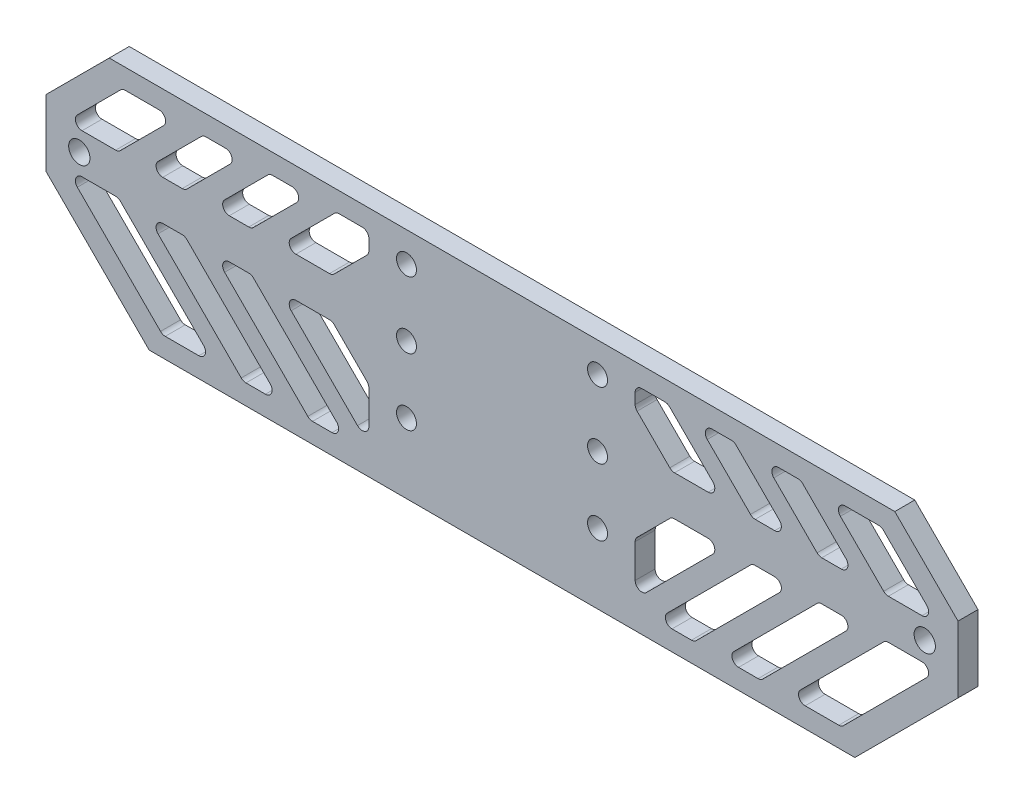
SolidWorks part; units mm, degrees
material "Thornel Mat VMA"
ref_plane "前视基准面" through (0, 0, 0) normal (0, 0, 1) x (1, 0, 0)
ref_plane "上视基准面" through (0, 0, 0) normal (0, 1, 0) x (1, 0, 0)
ref_plane "右视基准面" through (0, 0, 0) normal (1, 0, 0) x (0, 0, -1)
sketch "草图1" plane through (0, 0, 0) normal (0, 0, 1) x (1, 0, 0)
  line L1 (-16.35, 14.5) -> (16.35, 14.5)
  line L2 (-16.35, 14.5) -> (-16.35, -14.5)
  line L3 (-16.35, -14.5) -> (16.35, -14.5)
  line L4 (16.35, 14.5) -> (16.35, -14.5)
  line L5 (-16.35, 14.5) -> (16.35, -14.5) construction
  line L6 (-16.35, -14.5) -> (16.35, 14.5) construction
  line L7 (-14.35, 10) -> (14.35, 10) construction
  line L8 (-14.35, 10) -> (-14.35, -10) construction
  line L9 (-14.35, -10) -> (14.35, -10) construction
  line L10 (14.35, 10) -> (14.35, -10) construction
  line L11 (-14.35, 10) -> (14.35, -10) construction
  line L12 (-14.35, -10) -> (14.35, 10) construction
  circle A0 centre (-14.35, -10) radius 1.5
  circle A1 centre (-14.35, 10) radius 1.5
  circle A2 centre (14.35, 10) radius 1.5
  circle A3 centre (14.35, -10) radius 1.5
  circle A4 centre (-14.35, 0) radius 1.5
  circle A5 centre (14.35, 0) radius 1.5
  point P0 (0, 0)
  point P6 (0, 0)
  dimension "D5" = 3
  dimension "D1" = 29
  dimension "D2" = 28.7
  dimension "D3" = 32.7
  dimension "D4" = 20
extrude "凸台-拉伸1" add sketch "草图1" along normal blind 3
chamfer "倒角1" distance 3 angle 45 4 edges at (16.35, -14.5, 1.5) (16.35, 14.5, 1.5) (-16.35, -14.5, 1.5) (-16.35, 14.5, 1.5)
sketch "草图2" plane through (0, 0, 3) normal (0, 0, 1) x (1, 0, 0)
  line L0 (-11, 7) -> (-8, 10)
  line L1 (-8, 10) -> (8, 10)
  line L2 (-11, 7) -> (-11, -7)
  line L3 (-8, -10) -> (8, -10)
  line L4 (11, 7) -> (11, -7)
  line L5 (-11, 10) -> (11, -10) construction
  line L6 (-11, -10) -> (11, 10) construction
  line L7 (8, 10) -> (11, 7)
  line L8 (-11, -7) -> (-8, -10)
  line L9 (8, -10) -> (11, -7)
  point P0 (0, 0)
  dimension "D1" = 22
  dimension "D2" = 20
extrude "切除-拉伸1" [suppressed] cut sketch "草图2" against normal through all
fillet "圆角1" [suppressed] radius 1
sketch "草图3" plane through (0, 0, 3) normal (0, 0, 1) x (1, 0, 0)
  line L1 (-68.5, 14.5) -> (68.5, 14.5)
  line L2 (-68.5, 14.5) -> (-68.5, -14.5)
  line L3 (-68.5, -14.5) -> (68.5, -14.5)
  line L4 (68.5, 14.5) -> (68.5, -14.5)
  line L5 (-68.5, 14.5) -> (68.5, -14.5) construction
  line L6 (-68.5, -14.5) -> (68.5, 14.5) construction
  line L8 (16.35, -11.5) -> (16.35, 11.5)
  line L9 (16.35, 11.5) -> (13.35, 14.5)
  line L10 (13.35, 14.5) -> (-13.35, 14.5)
  line L11 (-13.35, 14.5) -> (-16.35, 11.5)
  line L12 (-16.35, 11.5) -> (-16.35, -11.5)
  line L13 (-16.35, -11.5) -> (-13.35, -14.5)
  line L14 (-13.35, -14.5) -> (13.35, -14.5)
  line L15 (13.35, -14.5) -> (16.35, -11.5)
  line L16 (16.35, -11.5) -> (16.35, 11.5)
  line L17 (16.35, 11.5) -> (13.35, 14.5)
  line L18 (13.35, 14.5) -> (-13.35, 14.5)
  line L19 (-13.35, 14.5) -> (-16.35, 11.5)
  line L20 (-16.35, 11.5) -> (-16.35, -11.5)
  line L21 (-16.35, -11.5) -> (-13.35, -14.5)
  line L22 (-13.35, -14.5) -> (13.35, -14.5)
  line L23 (13.35, -14.5) -> (16.35, -11.5)
  point P2 (0, 0)
  dimension "D2" = 137
  dimension "D1" = 0
extrude "凸台-拉伸2" add sketch "草图3" against normal up to surface (3 mm away) up to face at (0, 0, 0)
chamfer "倒角2" distance 9.5 4 edges at (68.5, -14.5, 1.5) (68.5, 14.5, 1.5) (-68.5, 14.5, 1.5) (-68.5, -14.5, 1.5)
sketch "草图4" plane through (0, 0, 0) normal (0, 0, -1) x (-1, 0, 0)
  line L0 (-59, -14.5) -> (-53, -20.5)
  line L1 (-53, -20.5) -> (53, -20.5)
  line L2 (53, -20.5) -> (59, -14.5)
  line L3 (59, -14.5) -> (-59, -14.5)
  line L4 (-68.5, -5) -> (-59, -14.5) construction
  line L5 (59, -14.5) -> (68.5, -5) construction
  dimension "D3" = 6
extrude "凸台-拉伸3" add sketch "草图4" against normal up to surface (3 mm away) up to face at (0, 0, 3)
sketch "草图6" plane through (0, 0, 0) normal (0, 0, -1) x (-1, 0, 0)
  circle A0 centre (-63.5, 0) radius 1.6
  dimension "D2" = 3.2
  dimension "D1" = 63.5
extrude "切除-拉伸2" cut sketch "草图6" against normal through all
sketch "草图7" plane through (0, 0, 0) normal (0, 0, -1) x (-1, 0, 0)
  line L24 (-65.5, 3) -> (-57, 11.5)
  line L29 (-65.5, -3) -> (-51, -17.5)
  line L30 (-55.5, -3) -> (-41, -17.5)
  line L32 (-68.5, 0) -> (0, 0)
  line L33 (-68.5, -5) -> (-68.5, 5) construction
  line L34 (-68.5, -3) -> (0, -3)
  line L35 (-68.5, 3) -> (0, 3)
  line L36 (-20, 14.5) -> (-20, -20.5)
  line L37 (-59, 14.5) -> (59, 14.5) construction
  line L38 (-53, -20.5) -> (53, -20.5) construction
  line L39 (-20, -20.5) -> (-53, -20.5)
  line L40 (-53, -20.5) -> (-68.5, -5)
  line L41 (-68.5, -5) -> (-68.5, 5)
  line L42 (-68.5, 5) -> (-59, 14.5)
  line L43 (-59, 14.5) -> (-20, 14.5)
  line L44 (-59, 14.5) -> (-68.5, 5) construction
  line L45 (-57.7574, 11.5) -> (-23, 11.5)
  line L47 (-23, -17.5) -> (-51.7574, -17.5)
  line L48 (-51.7574, -17.5) -> (-65.5, -3.7574)
  line L49 (-65.5, -3.7574) -> (-65.5, 3.7574)
  line L50 (-65.5, 3.7574) -> (-57.7574, 11.5)
  line L51 (-23, 11.5) -> (-20, 11.5)
  line L52 (-23, -17.5) -> (-20, -17.5)
  line L53 (-55.5, 3) -> (-47, 11.5)
  line L54 (-45.5, -3) -> (-31, -17.5)
  line L55 (-45.5, 3) -> (-37, 11.5)
  line L56 (-35.5, -3) -> (-21, -17.5)
  line L57 (-35.5, 3) -> (-27, 11.5)
  line L58 (-25.5, -3) -> (-11, -17.5)
  line L59 (-25.5, 3) -> (-17, 11.5)
  line L60 (-57.6213, -3) -> (-42.0607, -18.5607)
  line L61 (-47.6213, -3) -> (-32.0607, -18.5607)
  line L62 (-37.6213, -3) -> (-22.0607, -18.5607)
  line L63 (-34.4393, 1.9393) -> (-24.8787, 11.5)
  line L64 (-44.4393, 1.9393) -> (-34.8787, 11.5)
  line L65 (-54.4393, 1.9393) -> (-44.8787, 11.5)
  line L66 (-54.4393, -1.9393) -> (-38.8787, -17.5)
  line L67 (-44.4393, -1.9393) -> (-28.8787, -17.5)
  line L68 (-34.4393, -1.9393) -> (-19.9393, -16.4393)
  line L69 (-37.6213, 3) -> (-28.0607, 12.5607)
  line L70 (-47.6213, 3) -> (-38.0607, 12.5607)
  line L71 (-57.6213, 3) -> (-48.0607, 12.5607)
  line L72 (-56.5607, 4.0607) -> (-48.0607, 12.5607) construction
  line L73 (-54.4393, 1.9393) -> (-45.9393, 10.4393) construction
  line L74 (-36.5607, 4.0607) -> (-28.0607, 12.5607) construction
  line L75 (-44.4393, 1.9393) -> (-35.9393, 10.4393) construction
  line L76 (-34.4393, 1.9393) -> (-25.9393, 10.4393) construction
  line L77 (-54.4393, -1.9393) -> (-39.9393, -16.4393) construction
  line L78 (-46.5607, -4.0607) -> (-32.0607, -18.5607) construction
  line L79 (-44.4393, -1.9393) -> (-29.9393, -16.4393) construction
  line L80 (-36.5607, -4.0607) -> (-22.0607, -18.5607) construction
  line L81 (-46.5607, 4.0607) -> (-38.0607, 12.5607) construction
  line L82 (-56.5607, -4.0607) -> (-42.0607, -18.5607) construction
  line L113 (-23, 11.5) -> (-23, -17.5) construction
  dimension "D1" = 3
  dimension "D2" = 3
  dimension "D3" = 20
  dimension "D4" = 3
  dimension "D5" = 1.5
  dimension "D6" = 1.5
  dimension "D7" = 5
  dimension "D8" = 5.5
extrude "切除-拉伸4" cut sketch "草图7" against normal blind 10 contours L35 L71 L45 L24 | L60 L34 L29 L47 | L34 L66 L47 L61 | L35 L70 L45 L65 | L35 L69 L45 L64 | L34 L67 L47 L62 | L34 L68 L36 L58 | L63 L35 L59 L36 L51 L45
fillet "圆角2" radius 1 33 edges at (33.1213, -17.5, 1.5) (38.8787, -17.5, 1.5) (53.3787, -3, 1.5) (47.6213, -3, 1.5) (51, -17.5, 1.5) (65.5, -3, 1.5) (57.6213, -3, 1.5) (43.1213, -17.5, 1.5) (20, -8.5, 1.5) (20, -16.3787, 1.5) (33.3787, -3, 1.5) (25.5, -3, 1.5) (23.1213, -17.5, 1.5) (28.8787, -17.5, 1.5) (43.3787, -3, 1.5) (37.6213, -3, 1.5) (20, 11.5, 1.5) (20, 8.5, 1.5) (25.5, 3, 1.5) (33.3787, 3, 1.5) (24.8787, 11.5, 1.5) (57, 11.5, 1.5) (49.1213, 11.5, 1.5) (53.3787, 3, 1.5) (44.8787, 11.5, 1.5) (39.1213, 11.5, 1.5) (47.6213, 3, 1.5) (43.3787, 3, 1.5) (34.8787, 11.5, 1.5) (29.1213, 11.5, 1.5) (37.6213, 3, 1.5) (57.6213, 3, 1.5) (65.5, 3, 1.5)
mirror "镜向1" about plane through (0, 0, 0) normal (1, 0, 0) of "切除-拉伸2", "切除-拉伸4", "圆角2"
